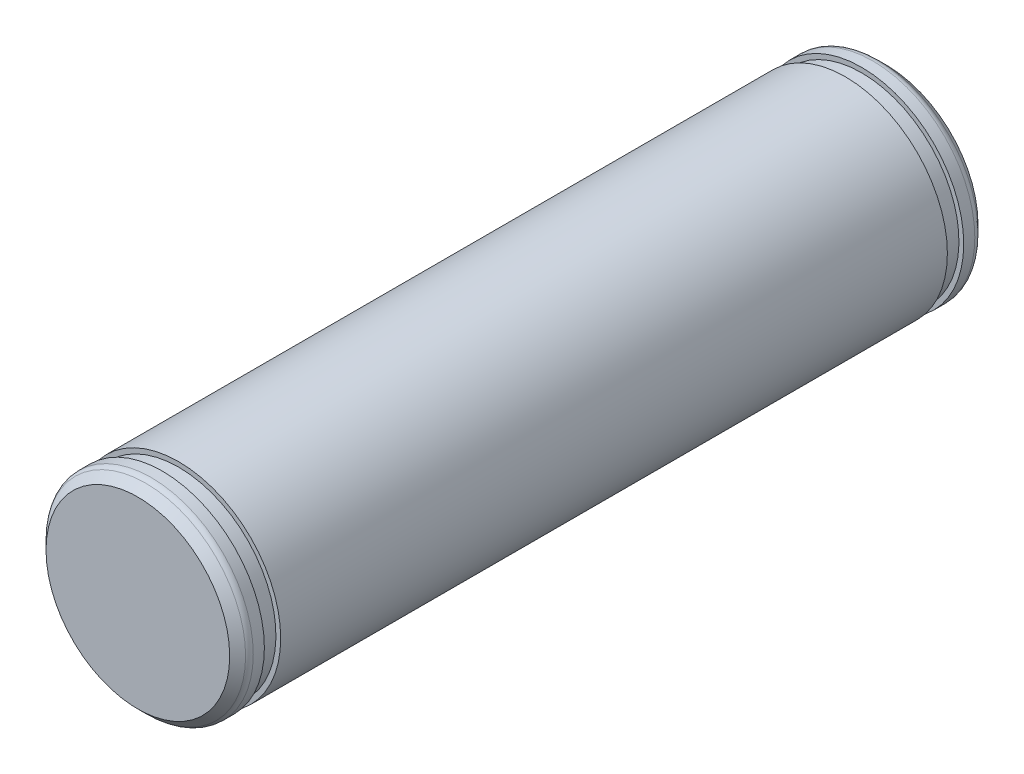
SolidWorks part; units mm, degrees
material "Plain Carbon Steel"
ref_plane "Front Plane" through (0, 0, 0) normal (0, 0, 1) x (1, 0, 0)
ref_plane "Top Plane" through (0, 0, 0) normal (0, 1, 0) x (1, 0, 0)
ref_plane "Right Plane" through (0, 0, 0) normal (1, 0, 0) x (0, 0, -1)
sketch "Sketch1" plane through (0, 0, 0) normal (0, 0, 1) x (1, 0, 0)
  line L0 (-7.5, 0) -> (7.5, 0) construction
  point P4 (0, 0)
  dimension "OD" = 15
sketch "Sketch2" plane through (0, 0, 0) normal (1, 0, 0) x (0, 0, -1)
  line L0 (27.5, 0) -> (-27.5, 0) construction
  line L1 (-27.5, 7.5) -> (-27.5, -7.5) construction
  line L2 (27.5, 7.5) -> (27.5, -7.5) construction
  point P0 (-10.25, 0)
  point P4 (0, 0)
  point P6 (10.25, 0)
  point P10 (27.5, 0)
  point P11 (0, 0)
  point P12 (-27.5, 0)
  point P13 (0, 0)
  dimension "Length" = 55
  dimension "D1" = 17.25
  dimension "D2" = 17.25
  dimension "D3" = 15
sketch "Sketch3" plane through (0, 0, 0) normal (0, 0, 1) x (1, 0, 0)
  circle A0 centre (0, 0) radius 7.5
extrude "Boss-Extrude1" add sketch "Sketch3" along normal mid plane 55
chamfer "Chamfer1" distance 0.75 angle 45 2 edges at (7.5, 0, 27.5) (7.5, 0, -27.5)
fillet "Fillet2" radius 0.5625 2 edges at (7.5, 0, 26.75) (7.5, 0, -26.75)
sketch "Sketch4" plane through (0, 0, 0) normal (1, 0, 0) x (0, 0, -1)
  line L0 (0, 0) -> (24.5, 0) construction
  line L1 (24.5, 0) -> (24.5, 7.15) construction
  line L2 (24.5, 7.15) -> (24.5, 7.5)
  line L3 (26.517, 7.5) -> (-26.517, 7.5) construction
  line L4 (24.5, 7.5) -> (25.7, 7.5)
  line L5 (25.7, 7.5) -> (25.7, 7.15)
  line L6 (25.7, 7.15) -> (24.5, 7.15)
  point P3 (23.3683, 6.8614)
  dimension "D1" = 0.35
  dimension "D2" = 1.2
  dimension "D3" = 24.5
revolve "Cut-Revolve1" cut sketch "Sketch4" angle 360 about L0
mirror "Mirror1" about plane through (0, 0, 0) normal (0, 0, 1) of "Cut-Revolve1"
equation "\"D1@Boss-Extrude1\"=\"Length@Sketch2\""
equation "\"D1@Chamfer1\"=\"OD@Sketch1\"*.05"
equation "\"D1@Fillet2\"=\"D1@Chamfer1\"*.75"
equation "\"D3@Sketch2\"=\"OD@Sketch1\""
equation "\"D1@Sketch2\"=\"OD@Sketch1\"*1.15"
equation "\"D2@Sketch2\"=\"D1@Sketch2\""
